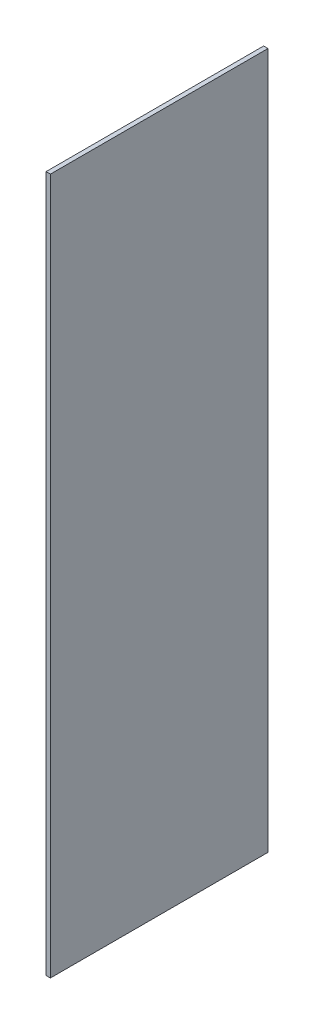
SolidWorks part; units mm, degrees
ref_plane "Front Plane" through (0, 0, 0) normal (0, 0, 1) x (1, 0, 0)
ref_plane "Top Plane" through (0, 0, 0) normal (0, 1, 0) x (1, 0, 0)
ref_plane "Right Plane" through (0, 0, 0) normal (1, 0, 0) x (0, 0, -1)
sketch "Sketch1" plane through (0, 0, 0) normal (0, 0, 1) x (1, 0, 0)
  line L1 (0, 0) -> (0.1, 0)
  line L2 (0, 0) -> (0, 16)
  line L3 (0, 16) -> (0.1, 16)
  line L4 (0.1, 0) -> (0.1, 16)
  dimension "D2" = 0.1
extrude "Boss-Extrude1" add sketch "Sketch1" along normal blind 5
equation "\"A.L\"= 0.07m"
equation "\"A.h\"= 0.007m"
equation "\"A.d\"= 0.005m"
equation "\"A.delta\"= 45.0001"
equation "\"A.w\"= 0m"
equation "\"A.v\"= 0.013m"
equation "\"A.s\"= 0.014m"
equation "\"A.t\"= 0.007m"
equation "\"B.L\"= 0.065m"
equation "\"B.h\"= 0.008m"
equation "\"B.s\"= 0.016m"
equation "\"B.t\"= 0.008m"
equation "\"C.h\"= 0.0065m"
equation "\"C.d\"= 0.005m"
equation "\"C.L\"= 0.05m"
equation "\"C.wmax\"= 0.003m"
equation "\"D.L\"= 0.06m"
equation "\"D.h\"= 0.008m"
equation "\"D.s\"= 0.012m"
equation "\"D.t\"= 0.008m"
equation "\"a_h\"= 0.0001m"
equation "\"a_d\"= 0.005m"
equation "\"a_L\"= 0.008m"
equation "\"b_h\"= 0.0004m"
equation "\"b_d\"= 0.005m"
equation "\"b_L\"= 0.007m"
equation "\"c_h\"= 0.0001m"
equation "\"c_d\"= 0.005m"
equation "\"c_L\"= 0.01m"
equation "\"d_h\"= 0.0001m"
equation "\"d_d\"= 0.005m"
equation "\"d_L\"= 0.01m"
equation "\"S.h\"= 0.015m"
equation "\"S.L\"= 0.09275m"
equation "\"D1@Sketch1\"=\"d_L\"+0.006"
equation "\"D2@Sketch1\"=\"d_h\""
equation "\"D1@Boss-Extrude1\"=\"d_d\""
